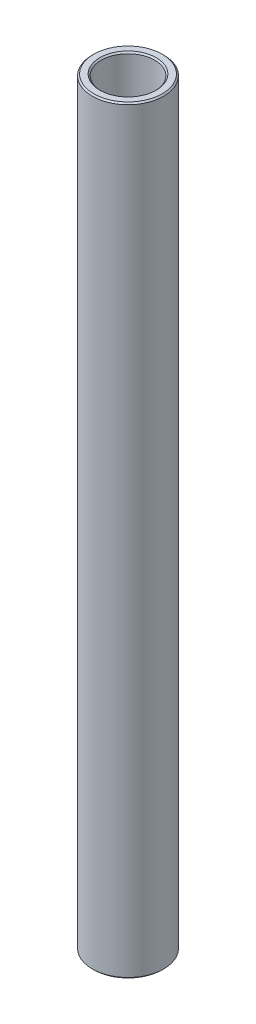
SolidWorks part; units mm, degrees
ref_plane "Front Plane" through (0, 0, 0) normal (0, 0, 1) x (1, 0, 0)
ref_plane "Top Plane" through (0, 0, 0) normal (0, 1, 0) x (1, 0, 0)
ref_plane "Right Plane" through (0, 0, 0) normal (1, 0, 0) x (0, 0, -1)
sketch "Sketch1" plane through (0, 0, 0) normal (0, 0, 1) x (1, 0, 0)
  line L0 (4.7625, 70.6437) -> (4.7625, 205.5816)
  line L1 (4.7625, 205.5816) -> (6.35, 205.5816)
  line L2 (6.35, 205.5816) -> (6.35, 70.6437)
  line L3 (6.35, 70.6437) -> (4.7625, 70.6437)
  line L4 (120.0875, 79.3749) -> (10.0875, 79.3749) construction
  line L6 (0, 61.1187) -> (0, 215.1066) construction
  dimension "D1" = 9.525
  dimension "D2" = 9.525
  dimension "D3" = 12.7
  dimension "D4" = 9.525
revolve "Revolve1" add sketch "Sketch1" angle 360 about L6
chamfer "Chamfer1" distance 0.254 angle 45 4 edges at (6.35, 205.5816, 0) (4.7625, 205.5816, 0) (4.7625, 70.6437, 0) (6.35, 70.6437, 0)
equation "\"D4@Sketch1\"=\"D1@Sketch1\""
